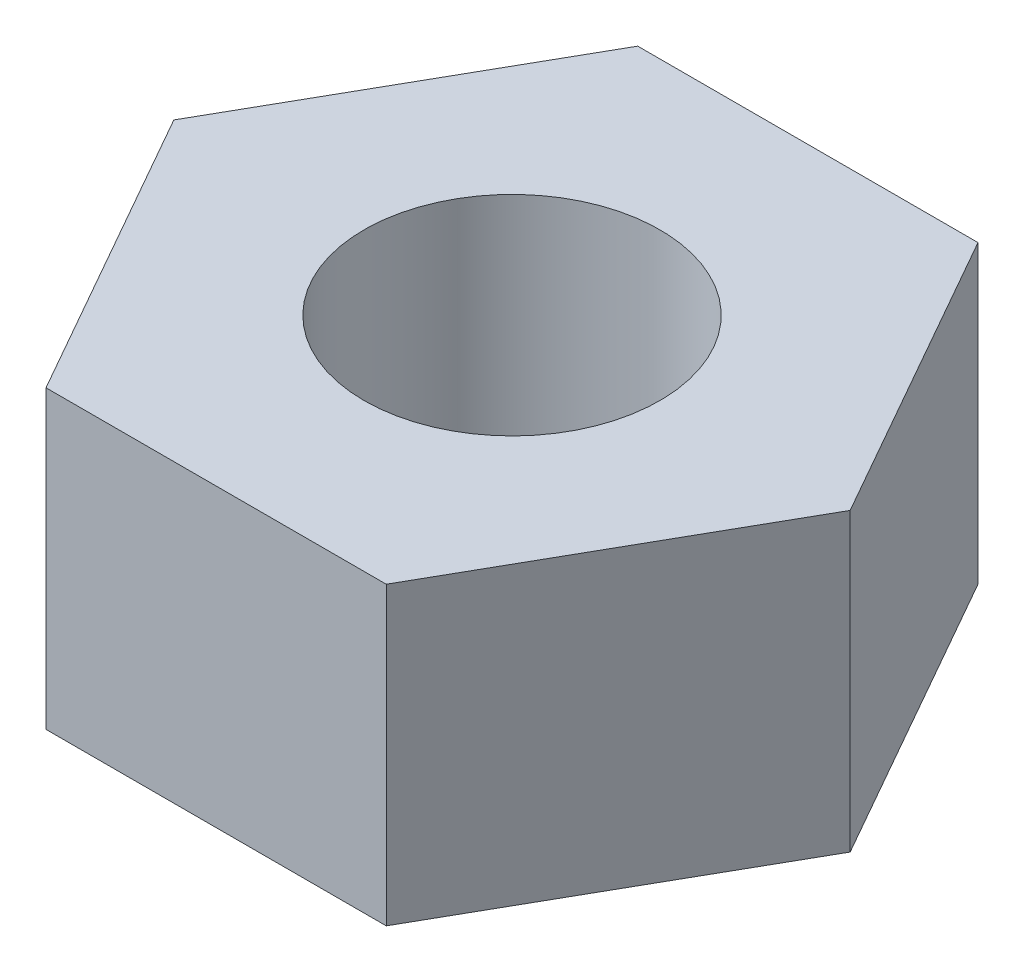
SolidWorks part; units mm, degrees
ref_plane "Front Plane" through (0, 0, 0) normal (0, 0, 1) x (1, 0, 0)
ref_plane "Top Plane" through (0, 0, 0) normal (0, 1, 0) x (1, 0, 0)
ref_plane "Right Plane" through (0, 0, 0) normal (1, 0, 0) x (0, 0, -1)
sketch "Sketch1" plane through (0, 0, 0) normal (0, 1, 0) x (1, 0, 0)
  line L0 (-5.75, 10) -> (5.75, 10)
  line L1 (5.75, 10) -> (11.4289, 0)
  line L2 (11.4289, 0) -> (5.75, -10)
  line L3 (5.75, -10) -> (-5.75, -10)
  line L4 (-5.75, -10) -> (-11.4289, 0)
  line L5 (-11.4289, 0) -> (-5.75, 10)
  circle A0 centre (0, 0) radius 5
  dimension "D4" = 10
  dimension "D1" = 11.5
  dimension "D2" = 20
  dimension "D3" = 5.75
extrude "Boss-Extrude1" add sketch "Sketch1" along normal blind 10
